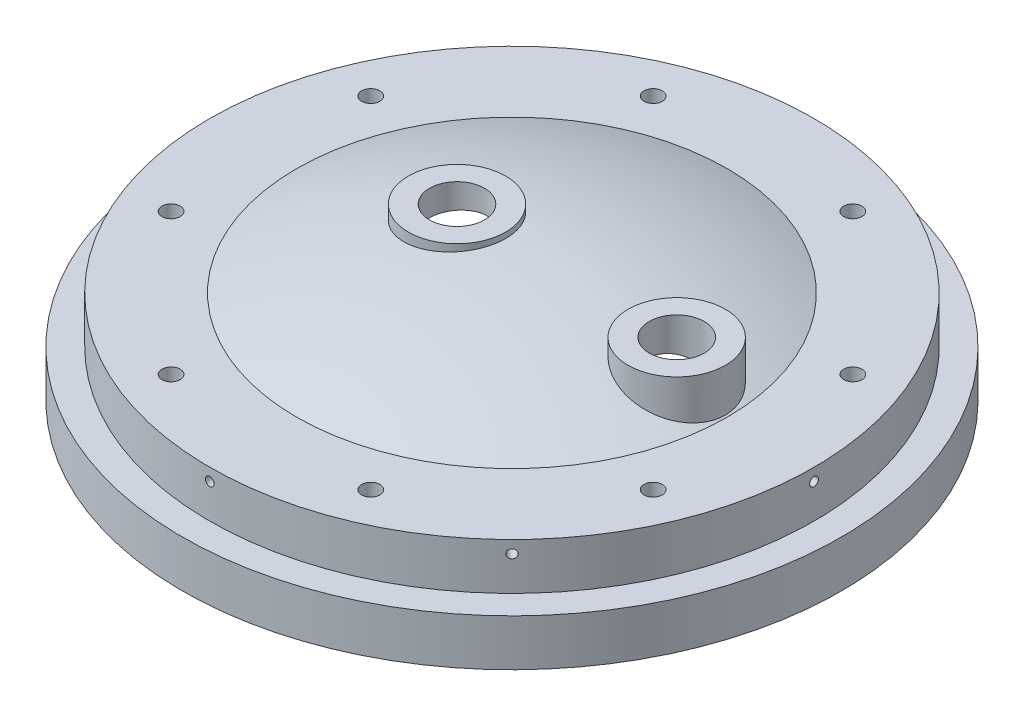
SolidWorks part; units mm, degrees
material "6061-T6 (SS)"
ref_plane "Front Plane" through (0, 0, 0) normal (0, 0, 1) x (1, 0, 0)
ref_plane "Top Plane" through (0, 0, 0) normal (0, 1, 0) x (1, 0, 0)
ref_plane "Right Plane" through (0, 0, 0) normal (1, 0, 0) x (0, 0, -1)
sketch "Sketch1" plane through (0, 0, 0) normal (0, 0, 1) x (1, 0, 0)
  line L0 (146.05, 0) -> (152.4, 0)
  line L1 (152.4, 0) -> (152.4, 21.59)
  line L2 (152.4, 21.59) -> (139.7, 21.59)
  line L3 (139.7, 21.59) -> (139.7, 43.18)
  line L4 (0, 63.5) -> (0, 57.15)
  line L5 (146.05, 0) -> (146.05, 9.4998)
  line L6 (139.7, 43.18) -> (99.5473, 43.18)
  arc A0 (0, 63.5) -> (99.5473, 43.18) centre (0, -190.5) cw
  arc A1 (0, 57.15) -> (146.05, 9.4998) centre (0, -190.5) cw
  point P12 (31.8203, -194.1697)
  dimension "D1" = 152.4
  dimension "D2" = 6.35
  dimension "D7" = 247.65
  dimension "D3" = 12.7
  dimension "D4" = 21.59
  dimension "D5" = 43.18
  dimension "D6" = 6.35
  dimension "D8" = 63.5
revolve "Revolve1" add sketch "Sketch1" angle 360 about L4
ref_plane "Plane1" through (139.7, 0, 0) normal (1, 0, 0) x (0, 0, -1)
hole_wizard "Tap Drill for #10-32 Tap1" positions "Sketch4" profile "Sketch5" hole size "#10-32" standard "ANSI Inch"
sketch "Sketch4" plane through (139.7, 0, 0) normal (1, 0, 0) x (0, 0, -1)
  line L0 (152.4, 21.59) -> (-152.4, 21.59) construction
  point P0 (0, 37.465)
  dimension "D1" = 15.875
sketch "Sketch5" plane through (139.7, 37.465, 0) normal (0, 1, 0) x (0, 0, -1)
  line L0 (0, 0) -> (0, 11.3733)
  line L1 (0, 11.3733) -> (2.0193, 10.16)
  line L2 (2.0193, 10.16) -> (2.0193, 0)
  line L5 (2.0193, 0) -> (0, 0)
  line L10 (0, 11.3733) -> (-2.0193, 10.16) construction
  line L11 (0, -6.35) -> (0, 107.95) construction
  dimension "Hole Dia." = 4.0386
  dimension "Hole Depth" = 10.16
  dimension "Drill Angle" = 118
pattern_circular "CirPattern1" count 8 over 360 about axis through (0, 63.5, 0) along (0, 1, 0) of "Tap Drill for #10-32 Tap1"
ref_plane "Plane2" through (0, 63.5, 0) normal (0, 1, 0) x (1, 0, 0)
sketch "Sketch6" plane through (0, 63.5, 0) normal (0, 1, 0) x (1, 0, 0)
  line L0 (-25.4, 0) -> (0, 0) construction
  circle A0 centre (-25.4, 0) radius 22.479
  dimension "D1" = 44.958
  dimension "D2" = 25.4
extrude "Boss-Extrude1" add sketch "Sketch6" along normal blind 2.54 and the other way up to next
sketch "Sketch7" plane through (0, 63.5, 0) normal (0, 1, 0) x (1, 0, 0)
  line L0 (76.2, 0) -> (0, 0) construction
  circle A0 centre (76.2, 0) radius 22.479
  dimension "D1" = 76.2
  dimension "D2" = 44.958
extrude "Boss-Extrude2" add sketch "Sketch7" against normal up to next
hole_wizard "Hole1" positions "Sketch8" profile "Sketch9" legacy
sketch "Sketch8" plane through (0, 66.04, 0) normal (0, 1, 0) x (1, 0, 0)
  point P0 (-25.4, 0)
sketch "Sketch9" plane through (-25.4, 66.04, 0) normal (1, 0, 0) x (0, 0, 1)
  line L0 (0, 0) -> (0, 25.4)
  line L1 (0, 25.4) -> (12.7, 25.4)
  line L2 (12.7, 25.4) -> (12.7, 0)
  line L3 (12.7, 0) -> (0, 0)
  line L4 (0, 110) -> (0, -10) construction
  dimension "Diameter" = 25.4
  dimension "Depth" = 25.4
hole_wizard "Hole2" positions "Sketch12" profile "Sketch13" legacy
sketch "Sketch12" plane through (0, 63.5, 0) normal (0, 1, 0) x (1, 0, 0)
  point P0 (76.2, 0)
sketch "Sketch13" plane through (76.2, 63.5, 0) normal (1, 0, 0) x (0, 0, 1)
  line L0 (0, 0) -> (0, 25.4)
  line L1 (0, 25.4) -> (12.7, 25.4)
  line L2 (12.7, 25.4) -> (12.7, 0)
  line L3 (12.7, 0) -> (0, 0)
  line L4 (0, 110) -> (0, -10) construction
  dimension "Diameter" = 25.4
  dimension "Depth" = 25.4
hole_wizard "3/8-24 Tapped Hole1" positions "Sketch15" profile "Sketch16" tap size "3/8-24" standard "ANSI Inch"
sketch "Sketch15" plane through (0, 43.18, 0) normal (0, 1, 0) x (1, 0, 0)
  line L0 (0, 0) -> (111.4661, 46.1708)
  line L2 (0, 0) -> (139.7, 0)
  circle A0 centre (0, 0) radius 139.7 construction
  point P0 (111.4661, 46.1708)
  dimension "D2" = 120.65
  dimension "D1" = 22.5
sketch "Sketch16" plane through (111.4661, 43.18, -46.1708) normal (1, 0, 0) x (0, 0, 1)
  line L0 (0, 0) -> (0, 12.1855)
  line L1 (0, 12.1855) -> (4.2164, 9.652)
  line L2 (4.2164, 9.652) -> (4.2164, 0)
  line L5 (4.2164, 0) -> (0, 0)
  line L10 (0, 12.1855) -> (-4.2164, 9.652) construction
  line L11 (0, -6.35) -> (0, 107.95) construction
  dimension "Tap Drill Dia." = 8.4328
  dimension "Tap Drill Depth" = 9.652
  dimension "Drill Angle" = 118
cosmetic thread "Hole Thread1" parameters "D1"=9.652, "D2"=9.525
pattern_circular "CirPattern2" count 8 over 360 about axis through (0, 0, 0) along (0, 1, 0) of "3/8-24 Tapped Hole1"
